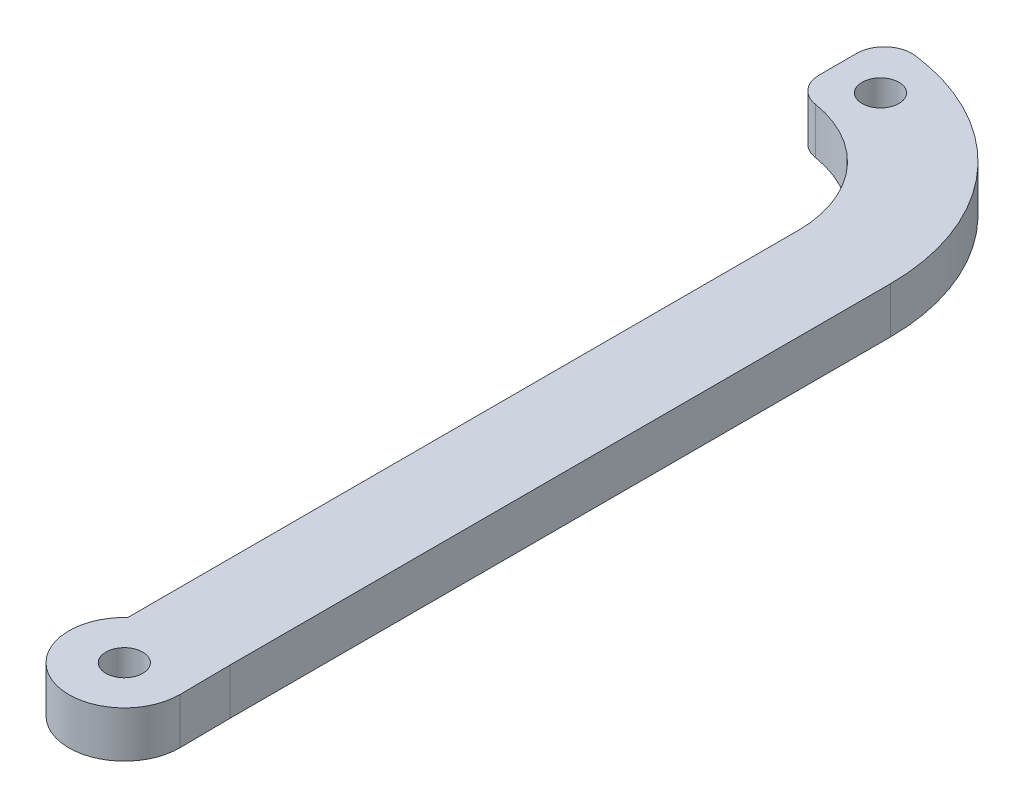
SolidWorks part; units mm, degrees
ref_plane "Front Plane" through (0, 0, 0) normal (0, 0, 1) x (1, 0, 0)
ref_plane "Top Plane" through (0, 0, 0) normal (0, 1, 0) x (1, 0, 0)
ref_plane "Right Plane" through (0, 0, 0) normal (1, 0, 0) x (0, 0, -1)
sketch "Sketch1" plane through (0, 0, 0) normal (0, 1, 0) x (1, 0, 0)
  line L0 (-4.055, -16.1207) -> (-4.055, -23.5199)
  line L1 (-4.055, -16.1207) -> (-4.055, 49.1132)
  line L2 (5.945, -22.4418) -> (6, -27.9418)
  line L3 (5.945, 2.0582) -> (5.945, -22.4418)
  line L4 (5.945, 2.0582) -> (5.945, 49.1132)
  line L7 (-17, 72.0582) -> (-17.5, 72.0582)
  line L9 (-17, 62.0582) -> (-17.5, 62.0582)
  line L10 (-17.5, 72.0582) -> (-17.5, 62.0582)
  arc A0 (-4.055, -23.5199) -> (5.9994, -27.8819) centre (0, -27.9418) ccw
  circle A1 centre (-12.5, 66.492) radius 2
  arc A4 (-17, 62.0582) -> (-4.055, 49.1132) centre (-17, 49.1132) cw
  circle A5 centre (0, -27.9418) radius 2
  arc A7 (-17, 72.0582) -> (5.945, 49.1132) centre (-17, 49.1132) cw
extrude "Boss-Extrude1" add sketch "Sketch1" along normal blind 5 contours A7 L7 L10 L9 A4 L1 L0 A0 L2 L3 L4 A5
fillet "Fillet1" radius 3 2 edges at (-17.5, 2.5, -62.0582) (-17.5, 2.5, -72.0582)
